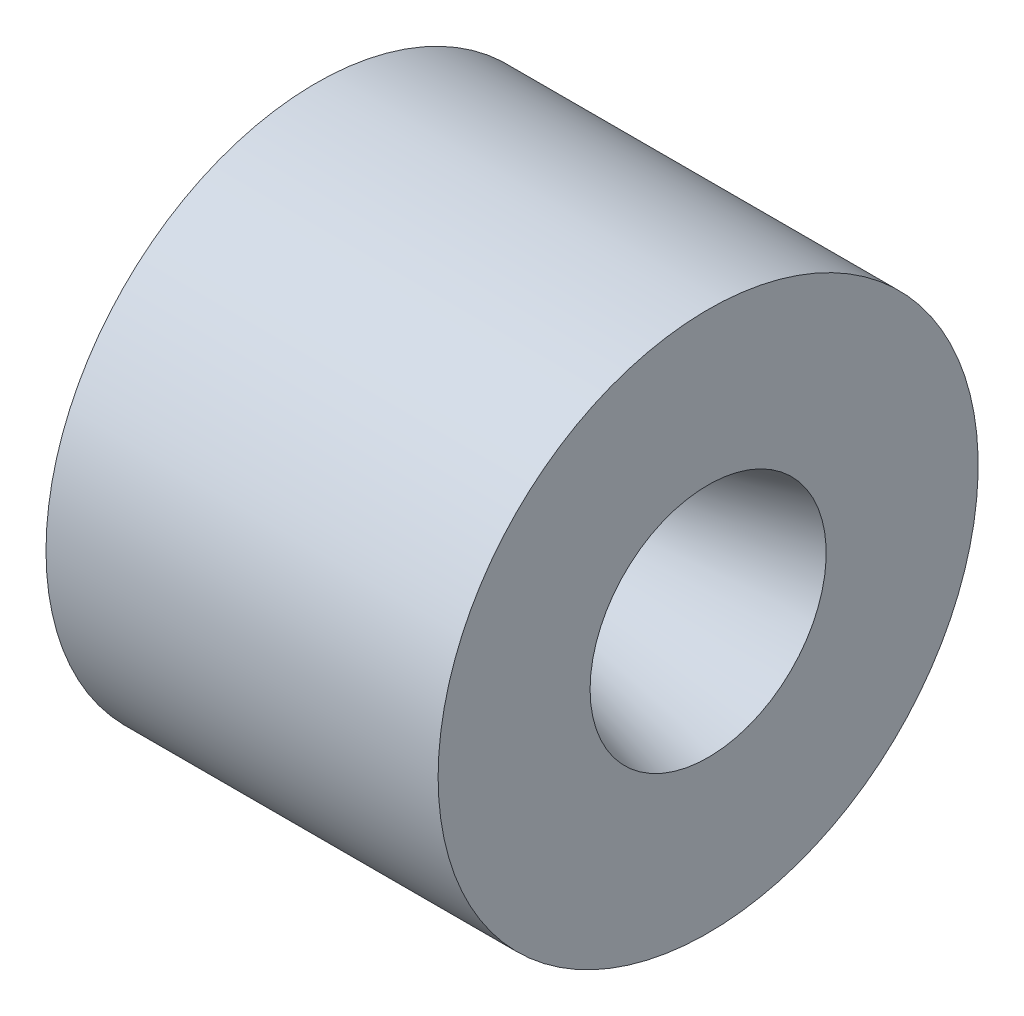
SolidWorks part; units mm, degrees
ref_plane "Front Plane" through (0, 0, 0) normal (0, 0, 1) x (1, 0, 0)
ref_plane "Top Plane" through (0, 0, 0) normal (0, 1, 0) x (1, 0, 0)
ref_plane "Right Plane" through (0, 0, 0) normal (1, 0, 0) x (0, 0, -1)
sketch "Sketch1" plane through (0, 0, 0) normal (0, 0, 1) x (1, 0, 0)
  line L0 (0, 0) -> (0, 24.13) construction
  line L1 (0, 24.13) -> (3.175, 24.13)
  line L2 (3.175, 24.13) -> (3.175, 15.875)
  line L3 (3.175, 15.875) -> (12.7, 6.35)
  line L4 (12.7, 6.35) -> (18.796, 6.35)
  line L5 (18.796, 6.35) -> (39.6507, 11.938)
  line L6 (39.6507, 11.938) -> (39.6507, 27.305)
  line L7 (39.6507, 27.305) -> (0, 27.305)
  line L8 (0, 27.305) -> (0, 24.13)
  line L9 (0, 0) -> (13.6933, 0) construction
  dimension "D1" = 135
  dimension "D2" = 24.13
  dimension "D3" = 15.875
  dimension "D4" = 11.938
  dimension "D5" = 165
  dimension "D6" = 6.35
  dimension "D7" = 6.096
  dimension "D8" = 3.175
  dimension "D9" = 27.305
  dimension "D10" = 39.6507
revolve "Revolve1" add sketch "Sketch1" angle 360 about L9
sketch "Sketch2" plane through (3.175, 0, 0) normal (-1, 0, 0) x (0, 0, 1)
  circle A0 centre (0, 0) radius 19.6723
  circle A1 centre (0, 0) radius 22.2885
  dimension "D1" = 39.3446
  dimension "D2" = 44.577
extrude "Cut-Extrude1" cut sketch "Sketch2" against normal blind 2.286
